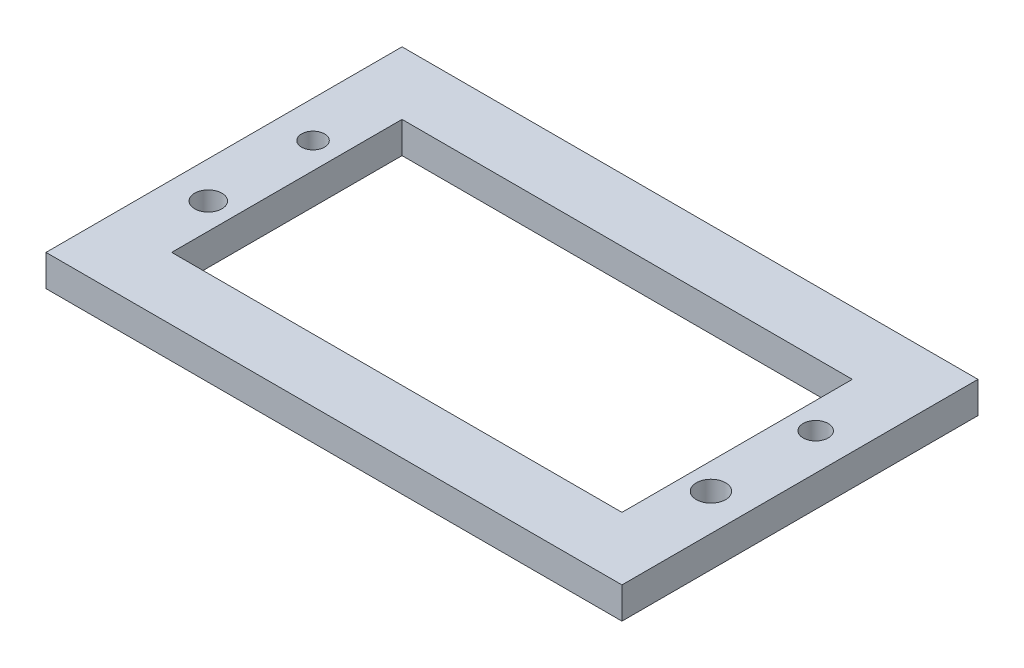
SolidWorks part; units mm, degrees
ref_plane "Front Plane" through (0, 0, 0) normal (0, 0, 1) x (1, 0, 0)
ref_plane "Top Plane" through (0, 0, 0) normal (0, 1, 0) x (1, 0, 0)
ref_plane "Right Plane" through (0, 0, 0) normal (1, 0, 0) x (0, 0, -1)
sketch "Sketch1" plane through (0, 0, 0) normal (0, 1, 0) x (1, 0, 0)
  line L0 (-21.5, 11) -> (21.5, 11)
  line L1 (-27.5, -17) -> (27.5, -17)
  line L2 (-27.5, -17) -> (-27.5, 17)
  line L3 (-27.5, 17) -> (27.5, 17)
  line L4 (27.5, -17) -> (27.5, 17)
  line L5 (-27.5, -17) -> (27.5, 17) construction
  line L6 (-27.5, 17) -> (27.5, -17) construction
  line L7 (21.5, -11) -> (21.5, 11)
  line L8 (-21.5, -11) -> (21.5, -11)
  line L9 (-21.5, -11) -> (-21.5, 11)
  circle A0 centre (-24, 5) radius 1.1
  circle A1 centre (-24, -5) radius 1.3
  circle A2 centre (24, 5) radius 1.2
  circle A3 centre (24, -5) radius 1.4
  point P0 (0, 0)
  point P18 (0, 0)
  point P19 (0, 0)
  point P20 (0, 0)
  point P21 (0, 0)
  point P22 (-23.9717, 6.6162)
  dimension "D4" = 2.6
  dimension "D5" = 2.2
  dimension "D6" = 2.8
  dimension "D7" = 2.4
  dimension "D2" = 43
  dimension "D3" = 22
  dimension "D8" = 48
  dimension "D9" = 10
  dimension "D10" = 10
  dimension "D11" = 5
  dimension "D12" = 2.5
  dimension "D1" = 6
extrude "Boss-Extrude1" add sketch "Sketch1" along normal blind 3
